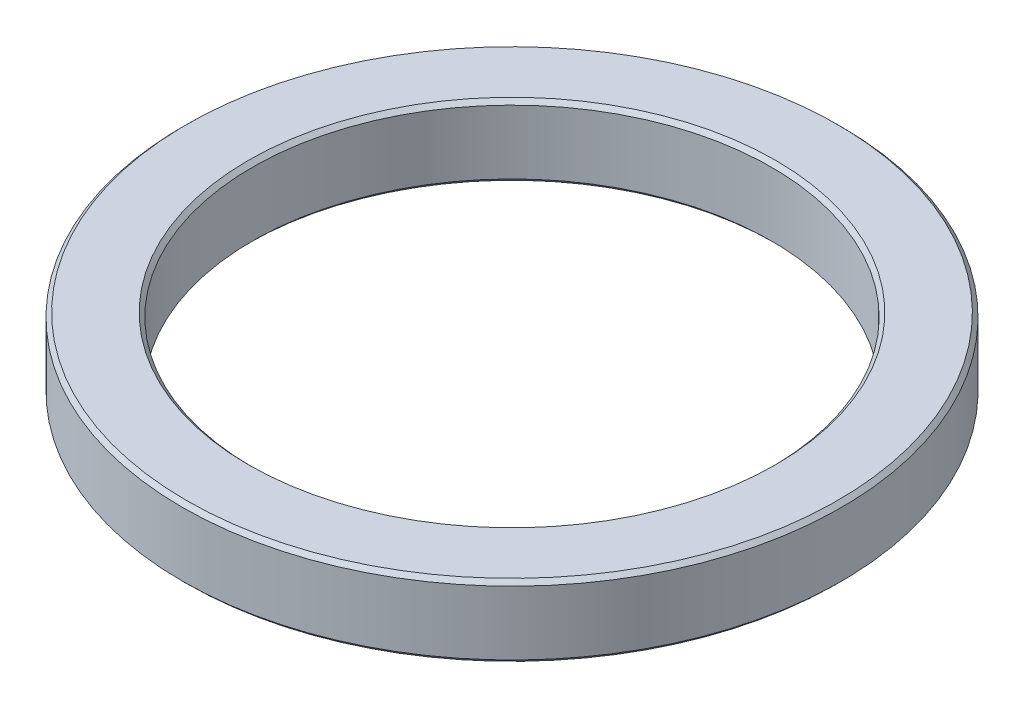
SolidWorks part; units mm, degrees
ref_plane "前视基准面" through (0, 0, 0) normal (0, 0, 1) x (1, 0, 0)
ref_plane "上视基准面" through (0, 0, 0) normal (0, 1, 0) x (1, 0, 0)
ref_plane "右视基准面" through (0, 0, 0) normal (1, 0, 0) x (0, 0, -1)
sketch "草图1" plane through (0, 0, 0) normal (0, 1, 0) x (1, 0, 0)
  circle A0 centre (0, 0) radius 82.5
  circle A1 centre (0, 0) radius 65
extrude "凸台-拉伸1" add sketch "草图1" along normal blind 18
chamfer "倒角1" distance 1 angle 45 4 edges at (0, 0, 82.5) (0, 18, 82.5) (0, 0, 65) (0, 18, 65)
